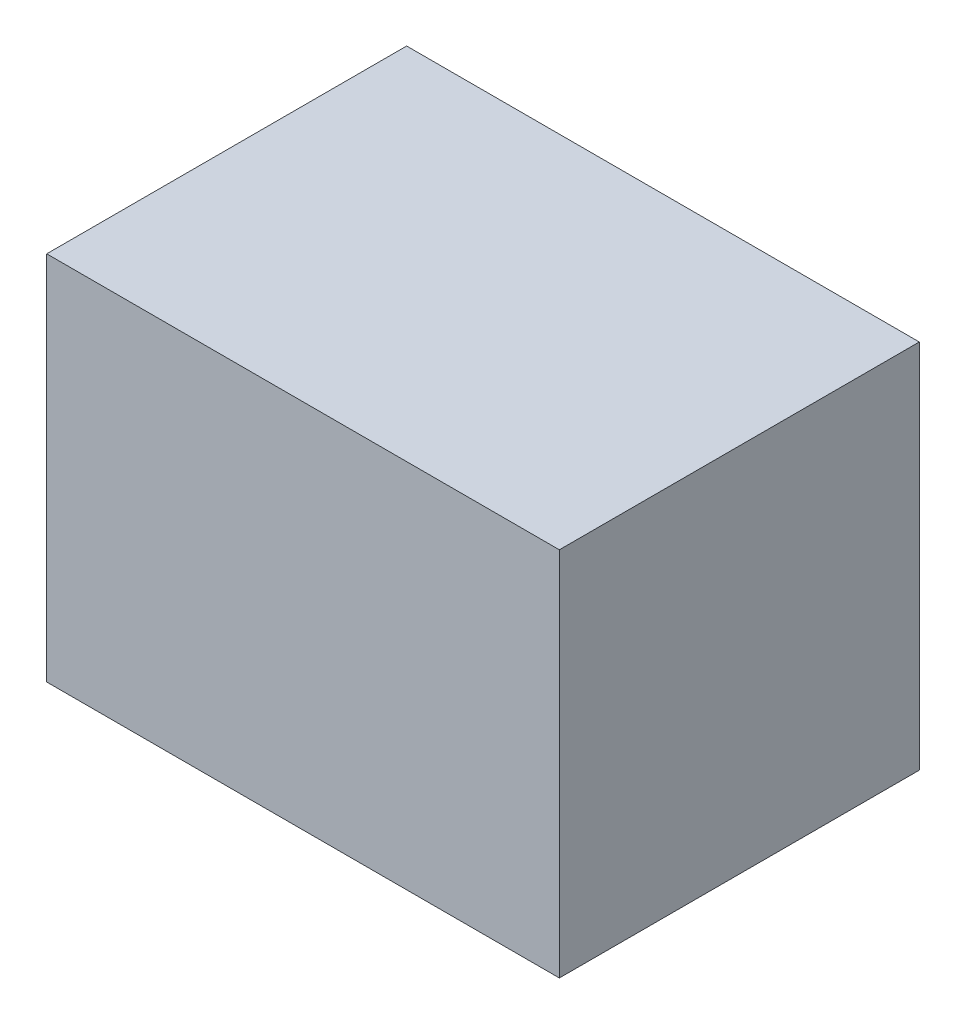
SolidWorks part; units mm, degrees
ref_plane "Front Plane" through (0, 0, 0) normal (0, 0, 1) x (1, 0, 0)
ref_plane "Top Plane" through (0, 0, 0) normal (0, 1, 0) x (1, 0, 0)
ref_plane "Right Plane" through (0, 0, 0) normal (1, 0, 0) x (0, 0, -1)
sketch "Sketch1" plane through (0, 0, 0) normal (0, 1, 0) x (1, 0, 0)
  line L1 (-0.0078, 1.7187) -> (4.6922, 1.7187)
  line L2 (-0.0078, 1.7187) -> (-0.0078, -1.5813)
  line L3 (-0.0078, -1.5813) -> (4.6922, -1.5813)
  line L4 (4.6922, 1.7187) -> (4.6922, -1.5813)
  dimension "D1" = 3.3
  dimension "D2" = 4.7
extrude "Boss-Extrude1" add sketch "Sketch1" along normal blind 3.4
